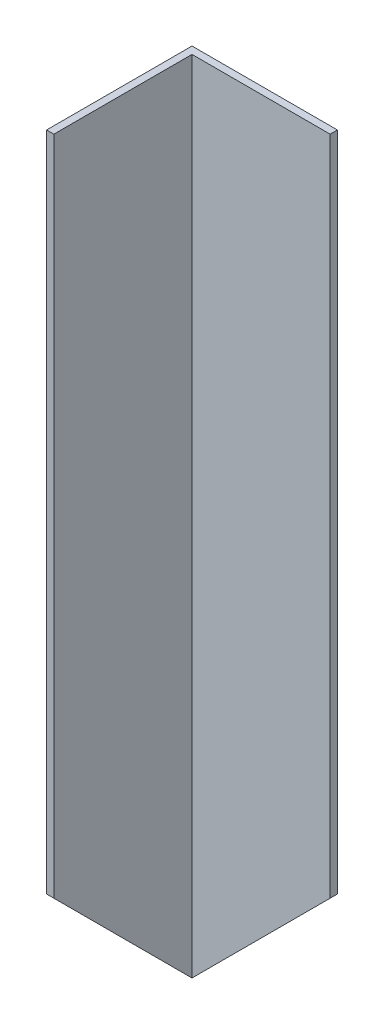
SolidWorks part; units mm, degrees
ref_plane "Plan de face" through (0, 0, 0) normal (0, 0, 1) x (1, 0, 0)
ref_plane "Plan de dessus" through (0, 0, 0) normal (0, 1, 0) x (1, 0, 0)
ref_plane "Plan de droite" through (0, 0, 0) normal (1, 0, 0) x (0, 0, -1)
sketch "Esquisse1" plane through (0, 0, 0) normal (0, 1, 0) x (1, 0, 0)
  line L1 (-20, 20.1136) -> (20, 20.1136)
  line L2 (-20, 20.1136) -> (-20, -19.8864)
  line L3 (-20, -19.8864) -> (-18, -19.8864)
  line L4 (20, 20.1136) -> (20, 18.1136)
  line L5 (-18, 18.1136) -> (20, 18.1136)
  line L6 (-18, 18.1136) -> (-18, -19.8864)
  dimension "D1" = 20
  dimension "D2" = 40
  dimension "D3" = 40
  dimension "D4" = 2
  dimension "D5" = 2
extrude "Boss.-Extru.1" add sketch "Esquisse1" along normal blind 222
sketch "Esquisse2" plane through (0, 0, -20.1136) normal (0, 0, -1) x (-1, 0, 0)
  line L0 (20, 0) -> (-20, 40)
  line L1 (20, 0) -> (-20, 0)
  line L2 (-20, 0) -> (-20, 40)
  dimension "D1" = 45
extrude "Enlèv. mat.-Extru.1" cut sketch "Esquisse2" against normal blind 590
sketch "Esquisse3" plane through (-20, 0, 0) normal (-1, 0, 0) x (0, 0, 1)
  line L0 (-20.1136, 0) -> (19.8864, 40)
  line L1 (19.8864, 222) -> (19.8864, 0) construction
  line L2 (19.8864, 40) -> (19.8864, 0)
  line L3 (19.8864, 0) -> (-20.1136, 0)
  dimension "D1" = 45
extrude "Enlèv. mat.-Extru.2" cut sketch "Esquisse3" against normal blind 590
